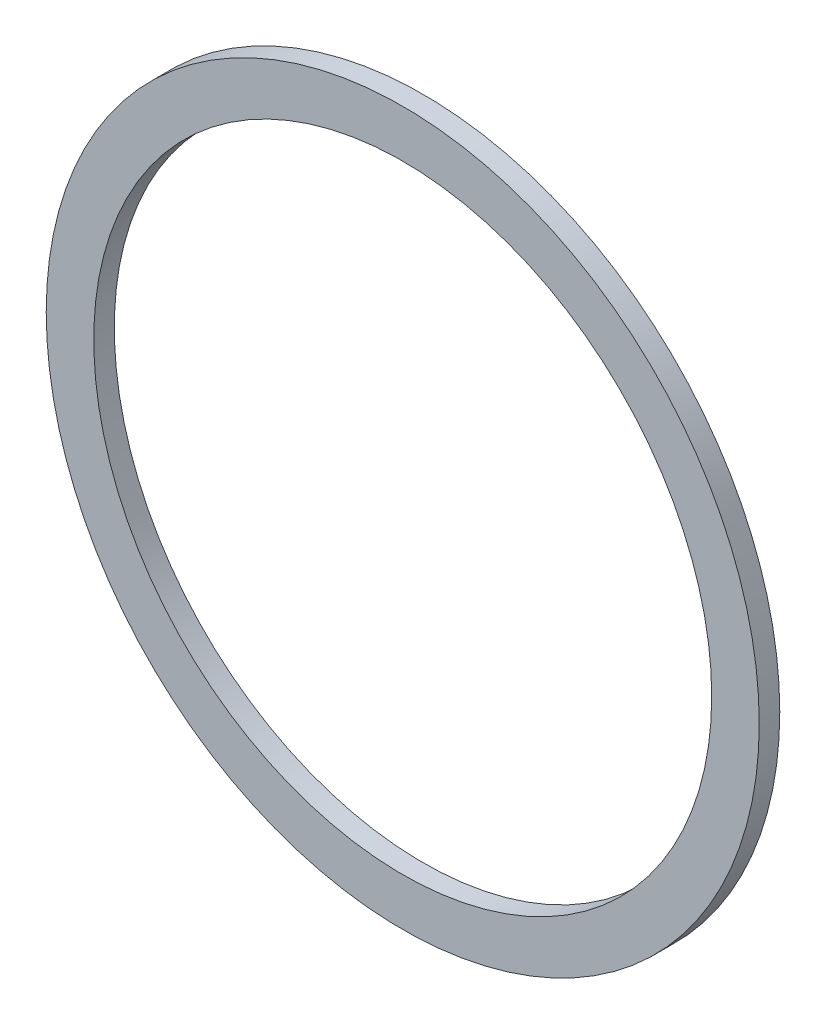
SolidWorks part; units mm, degrees
material "Balsa"
ref_plane "Front Plane" through (0, 0, 0) normal (0, 0, 1) x (1, 0, 0)
ref_plane "Top Plane" through (0, 0, 0) normal (0, 1, 0) x (1, 0, 0)
ref_plane "Right Plane" through (0, 0, 0) normal (1, 0, 0) x (0, 0, -1)
sketch "Sketch1" plane through (0, 0, 0) normal (0, 0, 1) x (1, 0, 0)
  circle A0 centre (0, 0) radius 75
  circle A1 centre (0, 0) radius 65
  dimension "D1" = 150
  dimension "D2" = 10
extrude "Boss-Extrude1" add sketch "Sketch1" along normal blind 4.318
